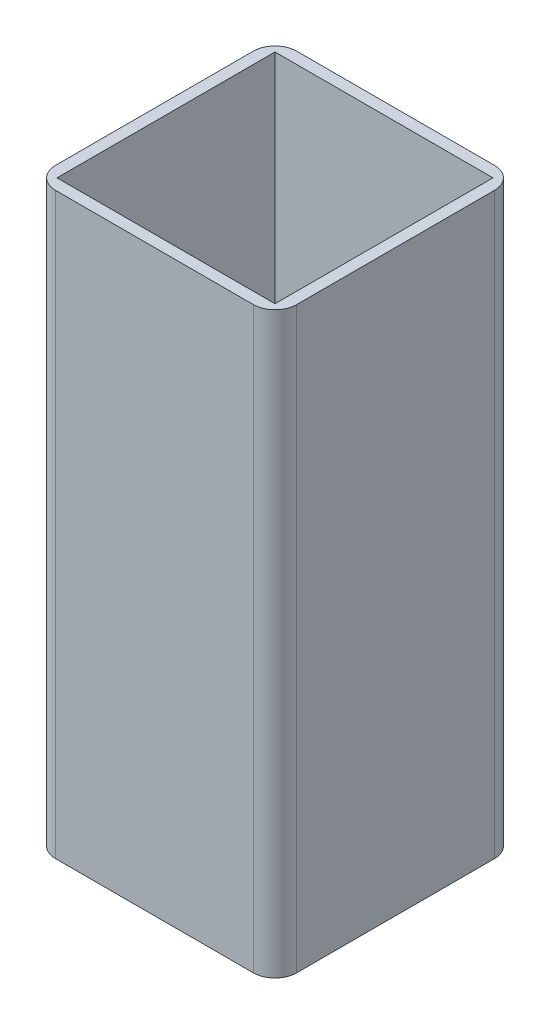
SolidWorks part; units mm, degrees
ref_plane "Front Plane" through (0, 0, 0) normal (0, 0, 1) x (1, 0, 0)
ref_plane "Top Plane" through (0, 0, 0) normal (0, 1, 0) x (1, 0, 0)
ref_plane "Right Plane" through (0, 0, 0) normal (1, 0, 0) x (0, 0, -1)
sketch "Sketch1" plane through (0, 0, 0) normal (0, 1, 0) x (1, 0, 0)
  line L0 (1.6, 31.7333) -> (31.7333, 31.7333)
  line L1 (0, 0) -> (33.3333, 0)
  line L2 (0, 0) -> (0, 33.3333)
  line L3 (0, 33.3333) -> (33.3333, 33.3333)
  line L4 (33.3333, 0) -> (33.3333, 33.3333)
  line L5 (31.7333, 1.6) -> (31.7333, 31.7333)
  line L6 (1.6, 1.6) -> (31.7333, 1.6)
  line L7 (1.6, 1.6) -> (1.6, 31.7333)
  dimension "D1" = 33.3333
  dimension "D2" = 1.6
extrude "Boss-Extrude1" add sketch "Sketch1" along normal blind 80
fillet "Fillet2" radius 3 4 edges at (0, 40, -33.3333) (0, 40, 0) (33.3333, 40, 0) (33.3333, 40, -33.3333)
scale "Scale1" scale about centroid uniform scaling yes scale factor 7.5
